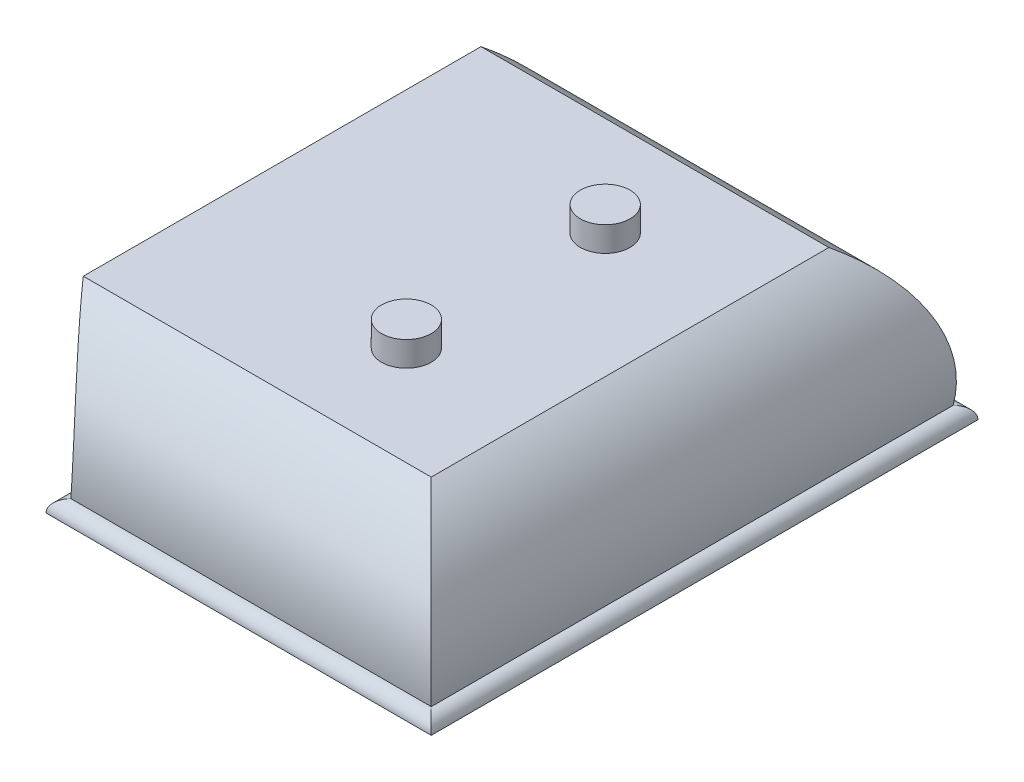
SolidWorks part; units mm, degrees
material "Oak"
ref_plane "Front Plane" through (0, 0, 0) normal (0, 0, 1) x (1, 0, 0)
ref_plane "Top Plane" through (0, 0, 0) normal (0, 1, 0) x (1, 0, 0)
ref_plane "Right Plane" through (0, 0, 0) normal (1, 0, 0) x (0, 0, -1)
sketch "Sketch1" plane through (0, 0, 0) normal (0, 1, 0) x (1, 0, 0)
  line L1 (-114.3, -50.8) -> (114.3, -50.8)
  line L2 (-114.3, -50.8) -> (-114.3, 50.8)
  line L3 (-114.3, 50.8) -> (114.3, 50.8)
  line L4 (114.3, -50.8) -> (114.3, 50.8)
  line L5 (-114.3, -50.8) -> (114.3, 50.8) construction
  line L6 (-114.3, 50.8) -> (114.3, -50.8) construction
  point P0 (0, 0)
  dimension "D1" = 228.6
  dimension "D2" = 101.6
extrude "Boss-Extrude1" add sketch "Sketch1" along normal blind 38.1
sketch "Sketch2" plane through (0, 0, 0) normal (0, -1, 0) x (1, 0, 0)
  line L1 (-133.35, -69.85) -> (133.35, -69.85)
  line L2 (-133.35, -69.85) -> (-133.35, 69.85)
  line L3 (-133.35, 69.85) -> (133.35, 69.85)
  line L4 (133.35, -69.85) -> (133.35, 69.85)
  line L5 (-133.35, -69.85) -> (133.35, 69.85) construction
  line L6 (-133.35, 69.85) -> (133.35, -69.85) construction
  point P0 (0, 0)
  dimension "D1" = 266.7
  dimension "D2" = 139.7
extrude "Boss-Extrude2" add sketch "Sketch2" along normal blind 38.1
sketch "Sketch4" plane through (0, 0, 0) normal (0, 0, 1) x (1, 0, 0)
  line L0 (38.1, -34.925) -> (-38.1, -34.925) construction
  line L2 (25.4, 0) -> (-25.4, 0)
  line L3 (-34.925, -38.1) -> (34.925, -38.1)
  line L4 (-133.35, -38.1) -> (133.35, -38.1) construction
  line L5 (3.9586, -27.5685) -> (-3.9586, -27.5685) construction
  line L6 (114.3, 0) -> (138.626, 8.3817)
  line L7 (138.626, 8.3817) -> (149.8507, -24.1953)
  line L8 (149.8507, -24.1953) -> (133.35, -38.1)
  line L9 (133.35, -38.1) -> (-133.35, -38.1) construction
  line L10 (0, 0) -> (0, -38.1) construction
  line L11 (-149.8507, -24.1953) -> (-133.35, -38.1)
  line L12 (-138.626, 8.3817) -> (-149.8507, -24.1953)
  line L13 (-114.3, 0) -> (-138.626, 8.3817)
  arc A0 (38.1, -34.925) -> (25.4, 0) centre (3.9586, -27.5685) ccw
  arc A1 (-25.4, 0) -> (-38.1, -34.925) centre (-3.9586, -27.5685) ccw
  arc A2 (38.1, -34.925) -> (34.925, -38.1) centre (38.1, -38.1) ccw
  arc A3 (-34.925, -38.1) -> (-38.1, -34.925) centre (-38.1, -38.1) ccw
  arc A4 (114.3, 0) -> (130.175, -34.925) centre (95.6677, -29.5397) cw
  arc A5 (130.175, -34.925) -> (133.35, -38.1) centre (130.175, -38.1) cw
  arc A6 (-130.175, -34.925) -> (-133.35, -38.1) centre (-130.175, -38.1) ccw
  arc A7 (-114.3, 0) -> (-130.175, -34.925) centre (-95.6677, -29.5397) ccw
  point P0 (0, -38.1)
  point P6 (0, -27.5685)
  point P10 (0, -34.925)
  dimension "D4" = 34.925
  dimension "D1" = 50.8
  dimension "D2" = 69.85
  dimension "D3" = 76.2
extrude "Cut-Extrude1" cut sketch "Sketch4" against normal through all both and the other way through all
sketch "Sketch5" plane through (0, 0, 0) normal (1, 0, 0) x (0, 0, -1)
  line L0 (69.85, -34.925) -> (-69.85, -34.925) construction
  line L1 (69.85, -38.1) -> (-69.85, -38.1) construction
  line L2 (-69.85, -38.1) -> (-80.2677, -6.18)
  line L3 (-80.2677, -6.18) -> (-69.85, 0.8488)
  line L4 (-69.85, 0.8488) -> (-50.8, 0)
  line L5 (0, 0) -> (0, -38.1) construction
  line L6 (69.85, 0.8488) -> (50.8, 0)
  line L7 (80.2677, -6.18) -> (69.85, 0.8488)
  line L8 (69.85, -38.1) -> (80.2677, -6.18)
  arc A0 (-50.8, 0) -> (-66.675, -34.925) centre (-32.1677, -29.5397) ccw
  arc A1 (-66.675, -34.925) -> (-69.85, -38.1) centre (-66.675, -38.1) ccw
  arc A2 (66.675, -34.925) -> (69.85, -38.1) centre (66.675, -38.1) cw
  arc A3 (50.8, 0) -> (66.675, -34.925) centre (32.1677, -29.5397) cw
  dimension "D1" = 34.925
extrude "Cut-Extrude2" cut sketch "Sketch5" against normal through all both and the other way through all
sketch "Sketch7" plane through (0, 0, 0) normal (1, 0, 0) x (0, 0, -1)
  line L0 (-50.8, 38.1) -> (-50.8, 0) construction
  line L13 (0, 41.91) -> (0, -41.91) construction
  line L17 (-50.8, 38.1) -> (50.8, 38.1)
  line L18 (50.8, 0) -> (-50.8, 0)
  arc A0 (-50.8, 0) -> (-50.8, 6.35) centre (-50.8, 3.175) cw
  arc A1 (-50.8, 6.35) -> (-50.8, 31.75) centre (0, 19.05) cw
  arc A2 (-50.8, 31.75) -> (-50.8, 38.1) centre (-50.8, 34.925) cw
  arc A3 (-66.675, -34.925) -> (-69.85, -38.1) centre (-66.675, -38.1) ccw construction
  arc A10 (50.8, 31.75) -> (50.8, 38.1) centre (50.8, 34.925) ccw
  arc A11 (50.8, 6.35) -> (50.8, 31.75) centre (0, 19.05) ccw
  arc A12 (50.8, 0) -> (50.8, 6.35) centre (50.8, 3.175) ccw
extrude "Boss-Extrude3" add sketch "Sketch7" along normal mid plane 234.95
sketch "Sketch8" plane through (0, 0, 0) normal (0, 0, 1) x (1, 0, 0)
  line L4 (117.475, 6.35) -> (-117.475, 6.35) construction
  line L8 (117.475, 31.75) -> (-117.475, 31.75) construction
  line L10 (-114.3, 38.1) -> (-123.4683, 41.2876)
  line L11 (-123.4683, 41.2876) -> (-120.4912, -2.3172)
  line L12 (-120.4912, -2.3172) -> (-114.3, 0)
  line L13 (0, 0) -> (0, 38.1) construction
  line L14 (120.4912, -2.3172) -> (114.3, 0)
  line L15 (123.4683, 41.2876) -> (120.4912, -2.3172)
  line L16 (114.3, 38.1) -> (123.4683, 41.2876)
  arc A6 (-114.3, 0) -> (-114.3, 6.35) centre (-114.3, 3.175) cw
  arc A7 (-114.3, 6.35) -> (-114.3, 31.75) centre (-80.2623, 19.05) cw
  arc A8 (-114.3, 31.75) -> (-114.3, 38.1) centre (-114.3, 34.925) cw
  arc A9 (114.3, 31.75) -> (114.3, 38.1) centre (114.3, 34.925) ccw
  arc A10 (114.3, 6.35) -> (114.3, 31.75) centre (80.2623, 19.05) ccw
  arc A11 (114.3, 0) -> (114.3, 6.35) centre (114.3, 3.175) ccw
extrude "Cut-Extrude3" cut sketch "Sketch8" against normal through all both and the other way through all
sketch "Sketch9" plane through (0, 0, 0) normal (0, 0, 1) x (1, 0, 0)
  line L0 (-114.3, 38.1) -> (114.3, 38.1)
  line L1 (-114.3, 38.1) -> (114.3, 38.1) construction
  arc A0 (114.3, 31.75) -> (114.3, 38.1) centre (114.3, 34.925) ccw construction
  arc A1 (114.3, 38.1) -> (79.375, 63.5) centre (114.3, 74.8109) cw
  arc A2 (79.375, 63.5) -> (-79.375, 63.5) centre (0, 194.1143) cw
  arc A3 (-79.375, 63.5) -> (-114.3, 38.1) centre (-114.3, 74.8109) cw
  point P15 (0, 41.2729)
  dimension "D3" = 152.8413
  dimension "D1" = 158.75
  dimension "D2" = 25.4
extrude "Boss-Extrude6" add sketch "Sketch9" along normal mid plane 101.6 contours A2 A3 L0 A1
sketch "Sketch10" plane through (0, 0, 0) normal (1, 0, 0) x (0, 0, -1)
  line L0 (-50.8, 63.5) -> (50.8, 63.5) construction
  line L1 (25.4, 63.5) -> (50.8, 63.5)
  line L2 (50.8, 63.5) -> (50.8, 38.1)
  line L3 (0, 63.5) -> (0, 38.1) construction
  line L4 (-50.8, 38.1) -> (50.8, 38.1) construction
  line L5 (-50.8, 63.5) -> (-50.8, 38.1)
  line L6 (-25.4, 63.5) -> (-50.8, 63.5)
  arc A0 (50.8, 38.1) -> (25.4, 63.5) centre (71.701, 84.401) cw
  arc A1 (-50.8, 38.1) -> (-25.4, 63.5) centre (-71.701, 84.401) ccw
  dimension "D1" = 50.8
extrude "Cut-Extrude4" cut sketch "Sketch10" against normal through all both and the other way through all
ref_plane "Plane2" through (0, 63.5, 0) normal (0, -1, 0) x (-1, 0, 0)
ref_plane "Plane1" through (0, 0, 9.525) normal (0, 0, 1) x (1, 0, 0)
sketch "Sketch11" plane through (0, 0, 9.525) normal (0, 0, 1) x (1, 0, 0)
  line L0 (-79.375, 63.5) -> (-79.375, 68.58)
  line L1 (79.375, 68.58) -> (79.375, 63.5)
  arc A0 (-79.375, 68.58) -> (79.375, 68.58) centre (0, 194.1143) ccw
  arc A1 (79.375, 63.5) -> (-79.375, 63.5) centre (0, 122.9743) cw
  arc A2 (-79.375, 63.5) -> (79.375, 63.5) centre (0, 194.1143) ccw construction
  dimension "D1" = 5.08
extrude "Boss-Extrude7" add sketch "Sketch11" along normal blind 11.43
sketch "Sketch12" plane through (0, 63.5, 0) normal (0, -1, 0) x (-1, 0, 0)
  line L1 (-50.8, -22.225) -> (50.8, -22.225)
  line L2 (-50.8, -22.225) -> (-50.8, 22.225)
  line L3 (-50.8, 22.225) -> (50.8, 22.225)
  line L4 (50.8, -22.225) -> (50.8, 22.225)
  line L5 (-50.8, -22.225) -> (50.8, 22.225) construction
  line L6 (-50.8, 22.225) -> (50.8, -22.225) construction
  point P0 (0, 0)
  dimension "D1" = 101.6
  dimension "D2" = 44.45
extrude "Cut-Extrude5" cut sketch "Sketch12" along normal blind 57.15
sketch "Sketch13" plane through (0, 0, -22.225) normal (0, 0, 1) x (1, 0, 0)
  line L0 (-50.8, 6.35) -> (50.8, 6.35) construction
  line L1 (-19.05, 34.925) -> (6.35, 34.925)
  line L2 (-19.05, 34.925) -> (-19.05, 19.05)
  line L3 (-19.05, 19.05) -> (6.35, 19.05)
  line L4 (6.35, 34.925) -> (6.35, 19.05)
  dimension "D1" = 25.4
  dimension "D2" = 15.875
  dimension "D3" = 6.35
  dimension "D4" = 12.7
extrude "Cut-Extrude6" cut sketch "Sketch13" against normal blind 8.89
sketch "Sketch15" plane through (0, 0, 0) normal (0, 1, 0) x (1, 0, 0)
  line L0 (-82.55, 25.4) -> (-82.55, -25.4) construction
  line L1 (82.55, 25.4) -> (82.55, -25.4) construction
  line L2 (-82.55, 0) -> (82.55, 0) construction
  line L4 (-133.35, -69.85) -> (-133.35, 69.85) construction
  circle A0 centre (-82.55, 25.4) radius 6.35
  circle A1 centre (-82.55, -25.4) radius 6.35
  circle A2 centre (82.55, -25.4) radius 6.35
  circle A3 centre (82.55, 25.4) radius 6.35
  dimension "D1" = 12.7
  dimension "D2" = 50.8
  dimension "D3" = 50.8
sketch "Sketch14" plane through (0, 0, 0) normal (0, 0, 1) x (1, 0, 0)
  line L0 (25.4, 0) -> (114.3, 0) construction
  line L1 (-117.475, 73.3859) -> (117.475, 73.3859)
  line L2 (-117.475, 73.3859) -> (-117.475, 0)
  line L3 (-117.475, 0) -> (117.475, 0)
  line L4 (117.475, 73.3859) -> (117.475, 0)
  arc A0 (114.3, 0) -> (114.3, 6.35) centre (114.3, 3.175) ccw construction
  arc A1 (-114.3, 6.35) -> (-114.3, 0) centre (-114.3, 3.175) ccw construction
extrude "Cut-Extrude7" cut sketch "Sketch14" against normal through all both and the other way through all
extrude "Boss-Extrude8" add sketch "Sketch15" along normal blind 6.35
sketch "Sketch16" plane through (0, 0, 0) normal (0, 0, 1) x (1, 0, 0)
  line L1 (-138.0634, 8.0366) -> (-23.5434, 8.0366)
  line L2 (-138.0634, 8.0366) -> (-138.0634, -46.0419)
  line L3 (-138.0634, -46.0419) -> (-23.5434, -46.0419)
  line L4 (-23.5434, 8.0366) -> (-23.5434, -46.0419)
extrude "Cut-Extrude8" cut sketch "Sketch16" against normal through all both and the other way through all
